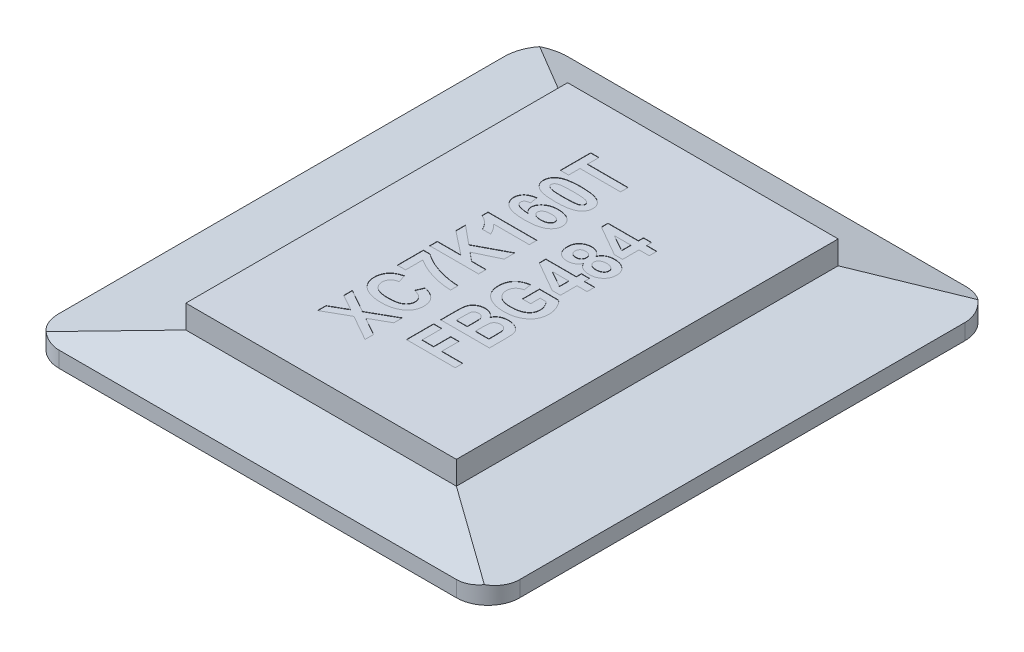
SolidWorks part; units mm, degrees
ref_plane "Front Plane" through (0, 0, 0) normal (0, 0, 1) x (1, 0, 0)
ref_plane "Top Plane" through (0, 0, 0) normal (0, 1, 0) x (1, 0, 0)
ref_plane "Right Plane" through (0, 0, 0) normal (1, 0, 0) x (0, 0, -1)
ref_plane "Plane1" through (0, 0.55, 0) normal (0, 1, 0) x (1, 0, 0)
sketch "Sketch1" plane through (0, 0, 0) normal (0, 1, 0) x (1, 0, 0)
  line L1 (-7.27, -8.025) -> (7.27, -8.025)
  line L2 (-7.27, -8.025) -> (-7.27, 8.025)
  line L3 (-7.27, 8.025) -> (7.27, 8.025)
  line L4 (7.27, -8.025) -> (7.27, 8.025)
  line L5 (-7.27, -8.025) -> (7.27, 8.025) construction
  line L6 (-7.27, 8.025) -> (7.27, -8.025) construction
  point P0 (0, 0)
  dimension "D1" = 14.54
  dimension "D2" = 16.05
sketch "Sketch2" plane through (0, 0.55, 0) normal (0, 1, 0) x (1, 0, 0)
  line L1 (-4.27, -6.025) -> (4.27, -6.025)
  line L2 (-4.27, -6.025) -> (-4.27, 6.025)
  line L3 (-4.27, 6.025) -> (4.27, 6.025)
  line L4 (4.27, -6.025) -> (4.27, 6.025)
  line L5 (-4.27, -6.025) -> (4.27, 6.025) construction
  line L6 (-4.27, 6.025) -> (4.27, -6.025) construction
  point P0 (0, 0)
  dimension "D1" = 8.54
  dimension "D2" = 12.05
loft "Loft1" add profiles "Sketch1", "Sketch2"
sketch "Sketch3" plane through (0, 0.55, 0) normal (0, 1, 0) x (1, 0, 0)
  line L1 (-4.27, -6.025) -> (4.27, -6.025)
  line L2 (-4.27, -6.025) -> (-4.27, 6.025)
  line L3 (-4.27, 6.025) -> (4.27, 6.025)
  line L4 (4.27, -6.025) -> (4.27, 6.025)
extrude "Boss-Extrude1" add sketch "Sketch3" along normal blind 0.735
sketch "Sketch4" plane through (0, 0, 0) normal (0, -1, 0) x (1, 0, 0)
  line L1 (-7.27, -8.025) -> (7.27, -8.025)
  line L2 (-7.27, -8.025) -> (-7.27, 8.025)
  line L3 (-7.27, 8.025) -> (7.27, 8.025)
  line L4 (7.27, -8.025) -> (7.27, 8.025)
extrude "Boss-Extrude2" add sketch "Sketch4" along normal blind 0.5
fillet "Fillet1" radius 1 4 edges
sketch "Sketch5" plane through (0, 1.285, 0) normal (0, 1, 0) x (1, 0, 0)
  line L0 (-0.4486, -4.1899) -> (-0.4486, 6.025) construction
  line L1 (1.7476, -3.6808) -> (1.7476, 6.025) construction
  line L3 (4.27, 6.025) -> (-4.27, 6.025) construction
  text T0 "XC7K160T" font "Arial Narrow" height in points 6
  text T1 "FBG484" font "Arial Narrow" height in points 6
  point P5 (-1.3254, -6.025)
  point P6 (-0.4744, -4.6369)
  point P8 (-1.3601, 6.025)
  point P11 (-0.521, -6.025)
  point P12 (0, 0)
  point P13 (2.1479, 6.025)
  point P14 (2.1701, -3.3718)
  point P15 (-0.4486, -4.1899)
  point P16 (1.7476, -3.6808)
extrude "Cut-Extrude1" cut sketch "Sketch5" against normal blind 0.01
